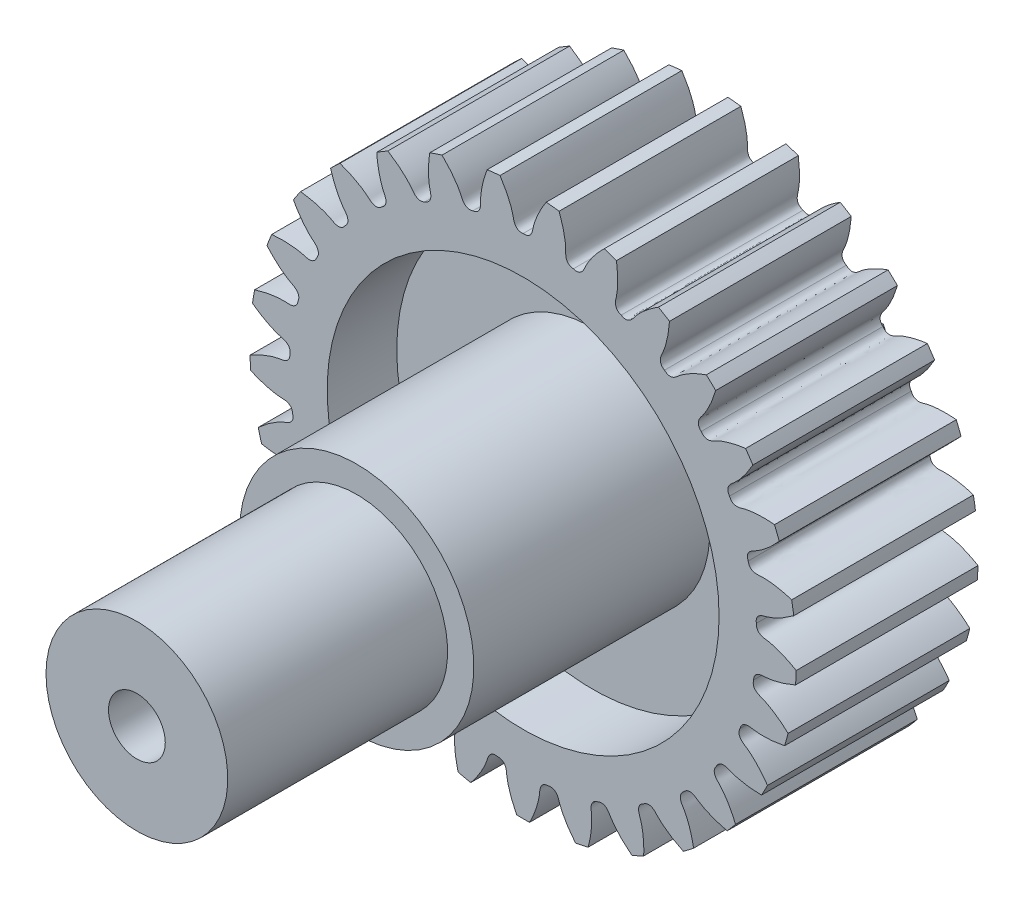
SolidWorks part; units mm, degrees
ref_plane "Front Plane" through (0, 0, 0) normal (0, 0, 1) x (1, 0, 0)
ref_plane "Top Plane" through (0, 0, 0) normal (0, 1, 0) x (1, 0, 0)
ref_plane "Right Plane" through (0, 0, 0) normal (1, 0, 0) x (0, 0, -1)
ref_axis "Axis1" through (0, 0, -88.99) along (0, 0, 1)
sketch "Gear-BaseSketch" plane through (0, 0, 0) normal (0, 0, 1) x (1, 0, 0)
  circle A0 centre (0, 0) radius 9.6209
  dimension "D1" = 19.2417
extrude "0.6207 Module, 18.0003mm P.D." add sketch "Gear-BaseSketch" along normal mid plane 6.4
sketch "Tooth-Sketch; Backlash: 0.0000mm" plane through (0, 0, 0) normal (0, 0, 1) x (1, 0, 0)
  line L0 (0, 0) -> (0, 12.6861) construction
  arc A0 (-0.8746, 9.6772) -> (0.8746, 9.6772) centre (0, 0) cw
  spline S0 degree 3 poles (-0.8746, 9.6772) (-0.8108, 9.5848) (-0.7231, 9.448) (-0.621, 9.2662) (-0.5579, 9.1431) (-0.5046, 9.0287) (-0.4602, 8.9233) (-0.4241, 8.8277) (-0.3955, 8.7421) (-0.3734, 8.6671) (-0.3572, 8.603) (-0.3471, 8.5562) (-0.3414, 8.5247) (-0.3374, 8.5048) (-0.3307, 8.4752) (-0.3192, 8.4352) (-0.2994, 8.3855) (-0.2724, 8.337) (-0.2333, 8.2891) (-0.1491, 8.2253) (-0.0586, 8.2184) (0, 8.224) knots 0 0 0 0 0.188221 0.272248 0.349553 0.420136 0.483997 0.541136 0.591552 0.635246 0.672218 0.702468 0.715453 0.726009 0.736359 0.766418 0.795747 0.825831 0.859099 0.898929 1 1 1 1
  spline S1 degree 3 poles (0.8746, 9.6772) (0.8108, 9.5848) (0.7231, 9.448) (0.621, 9.2662) (0.5579, 9.1431) (0.5046, 9.0287) (0.4602, 8.9233) (0.4241, 8.8277) (0.3955, 8.7421) (0.3734, 8.6671) (0.3572, 8.603) (0.3471, 8.5562) (0.3414, 8.5247) (0.3374, 8.5048) (0.3307, 8.4752) (0.3192, 8.4352) (0.2994, 8.3855) (0.2724, 8.337) (0.2333, 8.2891) (0.1491, 8.2253) (0.0586, 8.2184) (0, 8.224) knots 0 0 0 0 0.188221 0.272248 0.349553 0.420136 0.483997 0.541136 0.591552 0.635246 0.672218 0.702468 0.715453 0.726009 0.736359 0.766418 0.795747 0.825831 0.859099 0.898929 1 1 1 1
extrude "Tooth-Cut, Coarse Pitch Involute 20 deg" cut sketch "Tooth-Sketch; Backlash: 0.0000mm" against normal through all and the other way through all
pattern_circular "Tooth Pattern, 29 / 29" count 29 every 12.414 about axis through (0, 0, -88.99) along (0, 0, 1) of "Tooth-Cut, Coarse Pitch Involute 20 deg"
sketch "Sketch3" plane through (0, 0, 3.2) normal (0, 0, 1) x (1, 0, 0)
  circle A0 centre (0, 0) radius 6.9
  dimension "D1" = 13.8
extrude "Cut-Extrude5" cut sketch "Sketch3" against normal through all
sketch "Sketch4" plane through (0, 0, 0) normal (0, 1, 0) x (1, 0, 0)
  line L0 (0, 5.2) -> (3.25, 5.2)
  line L1 (0, 88.99) -> (0, -88.99) construction
  line L2 (3.25, 5.2) -> (3.25, 0.75)
  line L3 (3.25, 0.75) -> (6.9, 0.75)
  line L4 (6.9, 0.75) -> (6.9, -0.75)
  line L5 (6.9, -0.75) -> (4.125, -0.75)
  line L7 (4.125, -0.75) -> (4.125, -9.06)
  line L8 (4.125, -9.06) -> (3.2, -9.06)
  line L9 (3.2, -9.06) -> (3.2, -16.8)
  line L10 (3.2, -16.8) -> (0, -16.8)
  line L11 (0, -16.8) -> (0, 5.2)
  line L12 (6.9, 3.2) -> (-6.9, 3.2) construction
  line L13 (6.9, 3.2) -> (-6.9, 3.2) construction
  line L14 (-6.9, -3.2) -> (6.9, -3.2) construction
  line L15 (-6.9, -3.2) -> (6.9, -3.2) construction
  line L16 (6.9, 3.2) -> (6.9, -3.2) construction
  dimension "D1" = 3.25
  dimension "D2" = 2.45
  dimension "D3" = 2.45
  dimension "D4" = 2
  dimension "D5" = 4.125
  dimension "D6" = 3.2
  dimension "D7" = 12.26
  dimension "D8" = 20
revolve "Revolve1" add sketch "Sketch4" angle 360 about axis through (0, 0, -88.99) along (0, 0, 1)
sketch "Sketch5" plane through (0, 0, 16.8) normal (0, 0, 1) x (1, 0, 0)
  circle A0 centre (0, 0) radius 1
  dimension "D1" = 2
extrude "Cut-Extrude6" cut sketch "Sketch5" against normal through all
sketch "Sketch6" plane through (0, 0, -5.2) normal (0, 0, -1) x (-1, 0, 0)
  line L0 (1.7861, 0.9) -> (-1.7861, 0.9) construction
  line L1 (-1.7861, 0.9) -> (-0.4359, 0.9)
  line L2 (0.4359, 0.9) -> (1.7861, 0.9)
  arc A1 (1.7861, 0.9) -> (-1.7861, 0.9) centre (0, 0) cw
  circle A2 centre (0, 0) radius 2
  circle A3 centre (0, 0) radius 2 construction
  arc A4 (0.4359, 0.9) -> (-0.4359, 0.9) centre (0, 0) cw
  circle A5 centre (0, 0) radius 1 construction
  dimension "D2" = 0.9
  dimension "D1" = 1
extrude "Boss-Extrude2" add sketch "Sketch6" along normal blind 2.5
